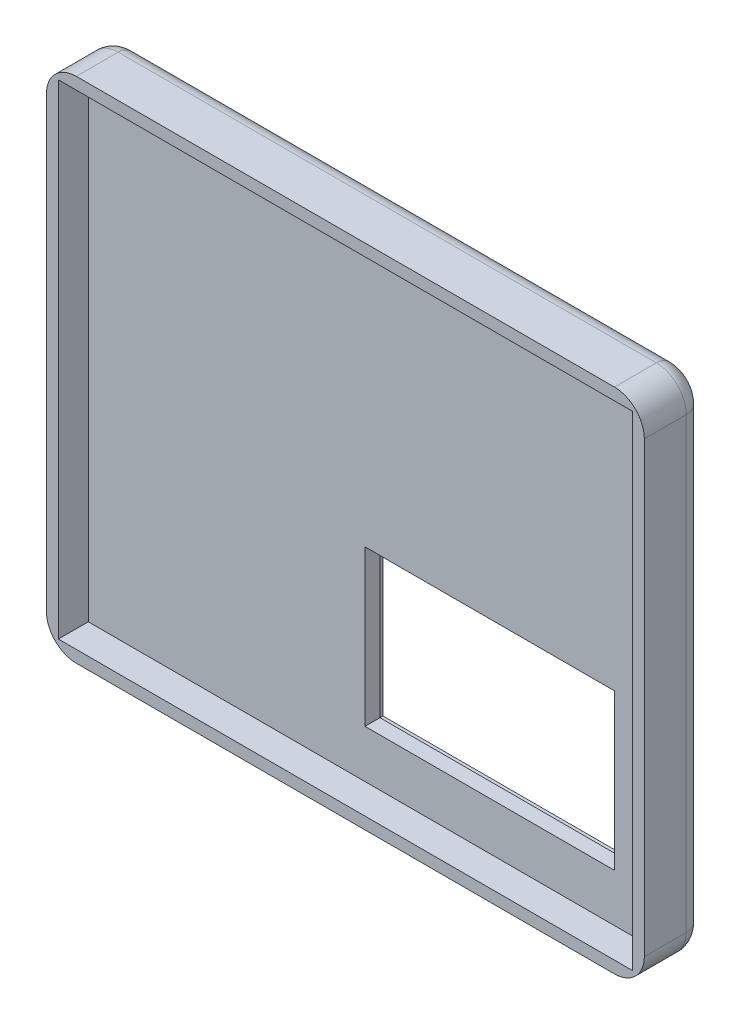
SolidWorks part; units mm, degrees
ref_plane "Front Plane" through (0, 0, 0) normal (0, 0, 1) x (1, 0, 0)
ref_plane "Top Plane" through (0, 0, 0) normal (0, 1, 0) x (1, 0, 0)
ref_plane "Right Plane" through (0, 0, 0) normal (1, 0, 0) x (0, 0, -1)
sketch "Sketch1" plane through (0, 0, 0) normal (0, 0, 1) x (1, 0, 0)
  line L1 (-50, 42.5) -> (50, 42.5)
  line L2 (-50, 42.5) -> (-50, -42.5)
  line L3 (-50, -42.5) -> (50, -42.5)
  line L4 (50, 42.5) -> (50, -42.5)
  line L5 (-50, 42.5) -> (50, -42.5) construction
  line L6 (-50, -42.5) -> (50, 42.5) construction
  point P0 (0, 0)
  dimension "D1" = 100
  dimension "D2" = 85
extrude "Boss-Extrude1" add sketch "Sketch1" along normal blind 5
sketch "Sketch4" plane through (0, 0, 0) normal (0, 0, -1) x (-1, 0, 0)
  line L0 (-50, 42.5) -> (50, 42.5) construction
  line L1 (-48, 40.5) -> (48, 40.5)
  line L2 (-48, 40.5) -> (-48, -40.5)
  line L3 (-48, -40.5) -> (48, -40.5)
  line L4 (48, 40.5) -> (48, -40.5)
  line L5 (-48, 40.5) -> (48, -40.5) construction
  line L6 (-48, -40.5) -> (48, 40.5) construction
  line L7 (50, -42.5) -> (-50, -42.5) construction
  line L8 (50, 42.5) -> (50, -42.5) construction
  line L9 (-50, -42.5) -> (-50, 42.5) construction
  line L11 (50, 42.5) -> (-50, 42.5)
  line L12 (50, 42.5) -> (50, -42.5)
  line L13 (50, -42.5) -> (-50, -42.5)
  line L14 (-50, 42.5) -> (-50, -42.5)
  line L15 (50, 42.5) -> (-50, -42.5) construction
  line L16 (50, -42.5) -> (-50, 42.5) construction
  point P0 (0, 0)
  point P14 (0, 0)
  dimension "D1" = 2
  dimension "D2" = 2
  dimension "D3" = 2
  dimension "D4" = 2
extrude "Boss-Extrude3" add sketch "Sketch4" against normal blind 10
fillet "Fillet1" radius 5 4 edges at (-50, -42.5, 5) (50, -42.5, 5) (50, 42.5, 5) (-50, 42.5, 5)
fillet "Fillet2" radius 3 8 edges at (48.5355, -41.0355, 0) (-48.5355, -41.0355, 0) (-48.5355, 41.0355, 0) (48.5355, 41.0355, 0) (0, -42.5, 0) (-50, 0, 0) (0, 42.5, 0) (50, 0, 0)
sketch "Sketch8" plane through (0, 0, 0) normal (0, 0, -1) x (-1, 0, 0)
  line L0 (-45, -39.5) -> (45, -39.5) construction
  line L1 (-42, -4.5) -> (3.72, -4.5)
  line L2 (-42, -4.5) -> (-42, -34.5)
  line L3 (-42, -34.5) -> (3.72, -34.5)
  line L4 (3.72, -4.5) -> (3.72, -34.5)
  line L5 (-47, 37.5) -> (-47, -37.5) construction
  dimension "D1" = 45.72
  dimension "D2" = 30
  dimension "D3" = 5
  dimension "D4" = 5
extrude "Cut-Extrude3" cut sketch "Sketch8" against normal blind 2.5
sketch "Sketch9" plane through (0, 0, 2.5) normal (0, 0, -1) x (-1, 0, 0)
  line L0 (3.72, -4.5) -> (-42, -4.5) construction
  line L1 (-40, -6.5) -> (1.72, -6.5)
  line L2 (-40, -6.5) -> (-40, -32.5)
  line L3 (-40, -32.5) -> (1.72, -32.5)
  line L4 (1.72, -6.5) -> (1.72, -32.5)
  line L5 (-42, -4.5) -> (-42, -34.5) construction
  line L6 (-42, -34.5) -> (3.72, -34.5) construction
  line L7 (3.72, -34.5) -> (3.72, -4.5) construction
  dimension "D1" = 2
  dimension "D2" = 2
  dimension "D3" = 2
  dimension "D4" = 2
extrude "Cut-Extrude4" cut sketch "Sketch9" against normal blind 100
